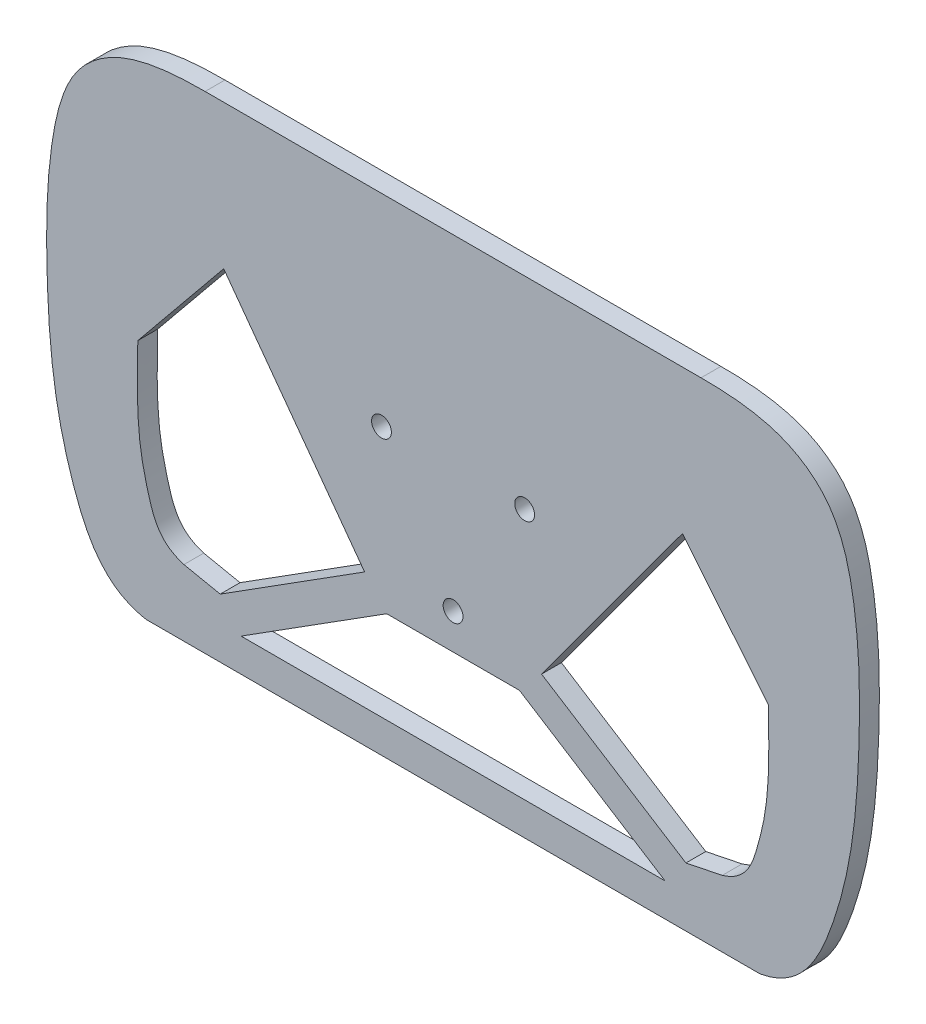
SolidWorks part; units mm, degrees
ref_plane "Front Plane" through (0, 0, 0) normal (0, 0, 1) x (1, 0, 0)
ref_plane "Top Plane" through (0, 0, 0) normal (0, 1, 0) x (1, 0, 0)
ref_plane "Right Plane" through (0, 0, 0) normal (1, 0, 0) x (0, 0, -1)
sketch "Sketch2" plane through (0, 0, 0) normal (0, 0, 1) x (1, 0, 0)
  line L0 (-37.2099, 73.2438) -> (312.1235, 73.2438) construction
sketch "Sketch1" plane through (0, 0, 0) normal (0, 0, 1) x (1, 0, 0)
  line L0 (0, 0) -> (0, 4.7682) construction
  line L2 (-21.6506, 12.5) -> (0, -25) construction
  line L3 (0, -25) -> (21.6506, 12.5) construction
  line L4 (21.6506, 12.5) -> (-21.6506, 12.5) construction
  line L18 (69.37, 29.9778) -> (95.3562, -1.8435)
  line L19 (92.8419, -73.6201) -> (-92.8419, -73.6201)
  line L21 (69.37, 29.9778) -> (26.7604, -28.1387)
  line L22 (26.7604, -28.1387) -> (70.423, -55.774)
  line L23 (70.423, -55.774) -> (81.4078, -53.5276)
  line L24 (-20.0704, -35.7391) -> (20.0704, -35.7391)
  line L25 (20.0704, -35.7391) -> (64.1211, -63.6201)
  line L26 (64.1211, -63.6201) -> (-64.1211, -63.6201)
  line L27 (-75, 73.5926) -> (75, 73.5926)
  line L29 (-125, 75) -> (125, 75) construction
  line L30 (-125, 75) -> (-125, -75) construction
  line L31 (-125, -75) -> (125, -75) construction
  line L32 (125, 75) -> (125, -75) construction
  line L41 (-20.0704, -35.7391) -> (-64.1211, -63.6201)
  line L42 (-69.37, 29.9778) -> (-95.3562, -1.8435)
  line L43 (-70.423, -55.774) -> (-81.4078, -53.5276)
  line L44 (-26.7604, -28.1387) -> (-70.423, -55.774)
  line L45 (-69.37, 29.9778) -> (-26.7604, -28.1387)
  circle A2 centre (-21.6506, 12.5) radius 3
  circle A3 centre (21.6506, 12.5) radius 3
  circle A4 centre (0, -25) radius 3
  circle A5 centre (0, 0) radius 25 construction
  spline S0 degree 3 poles (95.3562, -1.8435) (95.6715, -16.5555) (95.4951, -27.3473) (91.4565, -43.4485) (88.6166, -51.3764) (81.4078, -53.5276) knots 0 0 0 0 0.501053 0.67815 1 1 1 1
  spline S1 degree 3 poles (75, 73.5926) (82.6844, 73.5926) (97.8547, 72.8495) (116.5813, 59.7818) (122.879, 33.9195) (123.2357, 4.2325) (121.4222, -25.8302) (114.384, -53.8767) (105.2136, -71.4136) (92.8419, -73.6201) knots 0 0 0 0 0.136998 0.217327 0.350868 0.535495 0.700007 0.828084 1 1 1 1
  spline S2 degree 3 poles (-95.3562, -1.8435) (-95.6715, -16.5555) (-95.4951, -27.3473) (-91.4565, -43.4485) (-88.6166, -51.3764) (-81.4078, -53.5276) knots 0 0 0 0 0.501053 0.67815 1 1 1 1
  spline S5 degree 3 poles (-75, 73.5926) (-82.6844, 73.5926) (-97.8547, 72.8495) (-116.5813, 59.7818) (-122.879, 33.9195) (-123.2357, 4.2325) (-121.4222, -25.8302) (-114.384, -53.8767) (-105.2136, -71.4136) (-92.8419, -73.6201) knots 0 0 0 0 0.136998 0.217327 0.350868 0.535495 0.700007 0.828084 1 1 1 1
  point P16 (0, 73.5926)
  point P22 (0, -73.6201)
  point P33 (0, 0)
  point P34 (125, 0)
  point P36 (0, 75)
  point P38 (72.7799, 35.5137)
  point P51 (71.1835, 32.4144)
  point P52 (73.8741, 36.1313)
  point P53 (0, 0)
  point P54 (69.37, 30.5888)
  point P55 (64.1211, -63.6201)
  point P65 (0, 0)
  point P66 (100.3914, 69.7346)
  point P67 (112.6077, 60.9292)
  point P70 (0, -63.6201)
  point P71 (0, -35.7391)
  point P72 (0, 0)
  point P73 (0, 0)
  dimension "D1" = 250
  dimension "D2" = 6
  dimension "D3" = 50
  dimension "D5" = 10
  dimension "D7" = 150
  dimension "D4" = 150
  dimension "D6" = 10
extrude "Boss-Extrude1" add sketch "Sketch1" along normal blind 6
